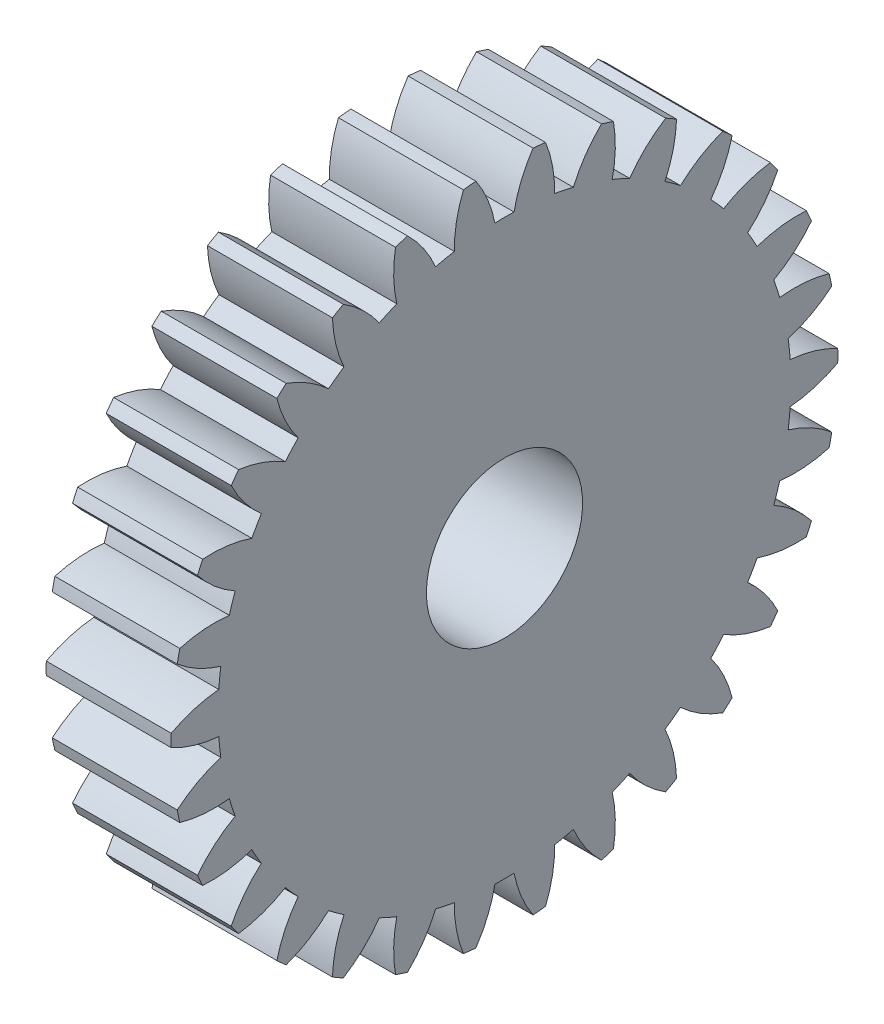
SolidWorks part; units mm, degrees
ref_plane "Plane1" through (0, 0, 0) normal (0, 0, 1) x (1, 0, 0)
ref_plane "Plane2" through (0, 0, 0) normal (0, 1, 0) x (1, 0, 0)
ref_plane "Plane3" through (0, 0, 0) normal (1, 0, 0) x (0, 0, -1)
other "Configuration Table"
sketch "HoldingSke" plane through (0, 0, 0) normal (0, 1, 0) x (1, 0, 0)
  line L0 (0, 0) -> (0.433, -0.25)
  line L1 (-15, 0) -> (100, 0) construction
  line L2 (0, 0) -> (-2.1039, 2.3779)
  line L3 (0, 0) -> (-11.863, 4.5341)
  line L4 (0, 0) -> (7.479, 4.318)
  line L5 (0, 0) -> (-46.8476, -17.4728)
  line L6 (0, 0) -> (-9.9476, -6.7116)
  line L7 (-2.1039, 2.3779) -> (8.6586, 51.2059)
  line L8 (-76.2, 54.61) -> (-73.9, 54.61)
  line L9 (-71.009, 38.7566) -> (-53.1078, 45.2721)
  line L10 (-76.2, 71.12) -> (104.1128, 71.12)
  line L11 (0, 0) -> (-12, 0)
  line L12 (-76.2, 101.6) -> (-76.133, 101.6)
  line L13 (24.9733, 27.94) -> (52.9518, 28.4284)
  line L14 (24.9733, 27.94) -> (24.9743, 27.94)
  line L15 (24.9733, 27.94) -> (100.4006, 29.5858)
  line L16 (-63.627, -2) -> (-12.827, -2)
  circle A0 centre (0, 0) radius 7.5
  circle A1 centre (0, 0) radius 27.499
  circle A2 centre (0, 0) radius 37.5
  circle A3 centre (0, 0) radius 7.5
  dimension "MHD" = 54.998
  dimension "Hub_dia" = 75
  dimension "Bore" = 15
  dimension "MBD" = 15
  dimension "Num_teeth" = 30
  dimension "Pitch" = 0.5
  dimension "Overall_len" = 50
  dimension "Show_teeth" = 30
  dimension "Thickness" = 12
  dimension "OAL" = 50.0001
  dimension "T_dim" = 2.3
  dimension "Ap" = 20
  dimension "H" = 19.05
  dimension "Pitch_radius" = 180.3128
  dimension "Width" = 12
  dimension "Backlash" = 0.067
  dimension "Addendum_fac" = 1
  dimension "Dedendum_fac" = 1.25
  dimension "Clearance_fac" = 0.25
  dimension "Dedendum_add" = 0.001
  dimension "Module" = 2
sketch "BasProSke" plane through (0, 0, 0) normal (0, 1, 0) x (1, 0, 0)
  line L0 (-10, 0) -> (60, 0) construction
  line L1 (0, 0) -> (0, 32)
  line L2 (0, 0) -> (12, 0)
  line L3 (12, 0) -> (12, 32)
  line L4 (12, 32) -> (0, 32)
  dimension "Thickness" = 12
  dimension "Diameter" = 64
revolve "Base-Revolve" add sketch "BasProSke" angle 360 about L0
sketch "TooCutSke" plane through (0, 0, 0) normal (1, 0, 0) x (0, 0, -1)
  line L1 (0, 0) -> (0, 107) construction
  line L2 (0, 0) -> (-1.6873, 29.9525) construction
  line L3 (0, 0) -> (-6.2643, 59.6013) construction
  line L4 (-1.6873, 29.9525) -> (-3.1322, 29.8007) construction
  arc A0 (0.9186, 27.4837) -> (-0.9186, 27.4837) centre (0, 0) ccw
  arc A1 (2.7618, 31.9061) -> (-2.7618, 31.9061) centre (0, 0) ccw
  circle A2 centre (0, 0) radius 30 construction
  circle A3 centre (0, 0) radius 28.1908 construction
  arc A4 (-0.9186, 27.4837) -> (-2.7618, 31.9061) centre (-12.6936, 25.1712) ccw
  arc A5 (2.7618, 31.9061) -> (0.9186, 27.4837) centre (12.6936, 25.1712) ccw
  dimension "Root_dia" = 54.998
  dimension "Overcut_dia" = 64.0508
  dimension "Pitch_dia" = 60
  dimension "Base_dia" = 56.3816
  dimension "Flank_rad" = 12
  dimension "Half_ang" = 6
  dimension "Half_CT" = 1.4528
extrude "ToothCut" cut sketch "TooCutSke" along normal through all
fillet "Breaks" [suppressed] radius 0.04
fillet "RootFillets" [suppressed] radius 0.501
pattern_circular "TeethCuts" count 30 every 12 about axis through (-10, 0, 0) along (1, 0, 0) of "ToothCut"
sketch "HubNeaOneSke" plane through (0, 0, 0) normal (-1, 0, 0) x (0, 0, 1)
  circle A0 centre (0, 0) radius 27.499
  dimension "Diameter" = 54.998
extrude "HubNearOne" [suppressed] add sketch "HubNeaOneSke" along normal blind 38.0001
sketch "HubNeaBotSke" plane through (0, 0, 0) normal (-1, 0, 0) x (0, 0, 1)
  circle A0 centre (0, 0) radius 27.499
  dimension "Diameter" = 54.998
extrude "HubNearBoth" [suppressed] add sketch "HubNeaBotSke" along normal blind 19
ref_plane "FarPln" through (12, 0, 0) normal (1, 0, 0) x (0, 0, -1)
sketch "HubFarSke" plane through (12, 0, 0) normal (1, 0, 0) x (0, 0, -1)
  circle A0 centre (0, 0) radius 27.499
  dimension "Diameter" = 54.998
extrude "HubFar" [suppressed] add sketch "HubFarSke" along normal blind 19
sketch "BorSke" plane through (0, 0, 0) normal (1, 0, 0) x (0, 0, -1)
  circle A0 centre (0, 0) radius 7.5
  dimension "Diameter" = 15
extrude "Bore" cut sketch "BorSke" along normal mid plane 100.0001
sketch "KeySke" plane through (0, 0, 0) normal (1, 0, 0) x (0, 0, -1)
  line L0 (-2.5, 0) -> (-2.5, 9.8)
  line L1 (-2.5, 9.8) -> (2.5, 9.8)
  line L2 (2.5, 9.8) -> (2.5, 0)
  line L3 (0, 0) -> (0, 34) construction
  line L4 (-2.5, 0) -> (2.5, 0)
  dimension "Offset" = 9.8
  dimension "Width" = 5
extrude "Keyway" [suppressed] cut sketch "KeySke" along normal mid plane 100.0001
pattern_circular "Keyway2" [suppressed] count 2 every 90 about axis through (-10, 0, 0) along (1, 0, 0)
equation "' \"Module@HoldingSke\" = 6.35"
equation "' \"Num_teeth@HoldingSke\" = 12"
equation "' \"Ap@HoldingSke\" =  20"
equation "' \"Ap@HoldingSke\" = 20"
equation "' \"Width@HoldingSke\" = 0.5 * 25.4"
equation "' \"Hub_dia@HoldingSke\"= 1 * 25.4"
equation "' \"Hub_dia@HoldingSke\" = 1 * 25.4"
equation "' \"Overall_len@HoldingSke\" = 1.0 * 25.4"
equation "' \"Bore@HoldingSke\" = 0.75 * 25.4"
equation "' \"T_dim@HoldingSke\" = 0.1 * 25.4"
equation "' \"Width@KeySke\" = 0.25 * 25.4"
equation "' \"Show_teeth@HoldingSke\" = 13"
equation "' \"Backlash@HoldingSke\" = 0.009 * 25.4"
equation "' \"Addendum_fac@HoldingSke\" = 1.0"
equation "' \"Dedendum_fac@HoldingSke\" = 1.25"
equation "' \"Dedendum_add@HoldingSke\" = 0.00005 * 25.4"
equation "' \"Clearance_fac@HoldingSke\" = 0.25"
equation "\"Pitch@HoldingSke\" = 1 / \"Module@HoldingSke\""
equation "\"Overcut_dia@TooCutSke\" = (\"Num_teeth@HoldingSke\" + 2 * \"Addendum_fac@HoldingSke\") / \"Pitch@HoldingSke\" + 0.002 * 25.4"
equation "\"Pitch_dia@TooCutSke\" = \"Num_teeth@HoldingSke\" / \"Pitch@HoldingSke\""
equation "\"Base_dia@TooCutSke\" = \"Num_teeth@HoldingSke\" / \"Pitch@HoldingSke\" * cos((\"Ap@HoldingSke\"  * 3.14159265 / 180))"
equation "\"Root_dia@TooCutSke\" = (\"Num_teeth@HoldingSke\" + 2) / \"Pitch@HoldingSke\" - 2 * (\"Addendum_fac@HoldingSke\" + \"Dedendum_fac@HoldingSke\") / \"Pitch@HoldingSke\" - \"Dedendum_add@HoldingSke\" * 2"
equation "\"Half_ang@TooCutSke\" = 180 / \"Num_teeth@HoldingSke\""
equation "\"Half_CT@TooCutSke\" = \"Num_teeth@HoldingSke\" / \"Pitch@HoldingSke\" * sin((3.14159265 / 2 / \"Num_teeth@HoldingSke\")) / 2 - 7 * \"Backlash@HoldingSke\" / 4"
equation "\"Flank_rad@TooCutSke\" = \"Num_teeth@HoldingSke\" / \"Pitch@HoldingSke\" / 5"
equation "\"Radius@RootFillets\" = \"Clearance_fac@HoldingSke\" / \"Pitch@HoldingSke\" + \"Dedendum_add@HoldingSke\""
equation "\"Break_rad@Breaks\" = 0.02 / \"Pitch@HoldingSke\""
equation "\"Thickness@HoldingSke\" = \"Width@HoldingSke\""
equation "\"OAL@HoldingSke\" = \"Thickness@HoldingSke\""
equation "\"MHD@HoldingSke\" = (\"Num_teeth@HoldingSke\" + 2) / \"Pitch@HoldingSke\" - 2 * (\"Addendum_fac@HoldingSke\" + \"Dedendum_fac@HoldingSke\")  / \"Pitch@HoldingSke\" - \"Dedendum_add@HoldingSke\" * 2"
equation "\"MBD@HoldingSke\" = (\"Num_teeth@HoldingSke\" + 2) / \"Pitch@HoldingSke\" - 2 * (\"Addendum_fac@HoldingSke\" + \"Dedendum_fac@HoldingSke\")  / \"Pitch@HoldingSke\" - \"Dedendum_add@HoldingSke\" * 2 - 0.002 * 25.4"
equation "\"MHD@HoldingSke\" = ((sgn( \"MHD@HoldingSke\" - \"Hub_dia@HoldingSke\" )-1)*( \"MHD@HoldingSke\" - \"Hub_dia@HoldingSke\" ))/-2+ \"Hub_dia@HoldingSke\""
equation "\"MBD@HoldingSke\" = ((sgn( \"MBD@HoldingSke\" - \"Bore@HoldingSke\" )-1)*( \"MBD@HoldingSke\" - \"Bore@HoldingSke\" ))/-2+ \"Bore@HoldingSke\""
equation "\"OAL@HoldingSke\" = ((sgn( \"OAL@HoldingSke\" - \"Overall_len@HoldingSke\" )+1)*( \"OAL@HoldingSke\" - \"Overall_len@HoldingSke\" ))/2 + \"Overall_len@HoldingSke\" + 0.000002 * 25.4"
equation "\"Num_teeth@TeethCuts\" = int( \"Show_teeth@HoldingSke\" ) + 1"
equation "\"Num_teeth@TeethCuts\" = ((sgn( \"Num_teeth@TeethCuts\" - \"Num_teeth@HoldingSke\" )-1)*( \"Num_teeth@TeethCuts\" - \"Num_teeth@HoldingSke\" ))/-2+ \"Num_teeth@HoldingSke\""
equation "\"Num_teeth@TeethCuts\" = ((sgn( \"Num_teeth@TeethCuts\" - 2.0)+1)*( \"Num_teeth@TeethCuts\" - 2.0))/2 +2.0"
equation "\"Angle@TeethCuts\" = 360.0 / \"Num_teeth@HoldingSke\""
equation "\"Diameter@BasProSke\" = (\"Num_teeth@HoldingSke\" + 2 * \"Addendum_fac@HoldingSke\") / \"Pitch@HoldingSke\""
equation "\"Thickness@BasProSke\"  = \"Thickness@HoldingSke\""
equation "' \"Fillet_rad@BasProSke\" =  \"Thickness@HoldingSke\" * 0.05"
equation "' \"Fillet_rad@BasProSke\" = \"Thickness@HoldingSke\" * 0.05"
equation "\"MHD@HoldingSke\" = ((sgn( \"MHD@HoldingSke\" - \"Root_dia@TooCutSke\" )-1)*( \"MHD@HoldingSke\" - \"Root_dia@TooCutSke\" ))/-2+ \"Root_dia@TooCutSke\""
equation "\"Diameter@HubNeaOneSke\" = \"MHD@HoldingSke\""
equation "\"Length@HubNearOne\" = \"OAL@HoldingSke\" - \"Thickness@BasProSke\""
equation "\"Diameter@HubNeaBotSke\" = \"MHD@HoldingSke\""
equation "\"Length@HubNearBoth\" = ( \"OAL@HoldingSke\" - \"Thickness@BasProSke\" ) / 2.0"
equation "\"Thickness@FarPln\" = \"Thickness@BasProSke\""
equation "\"Diameter@HubFarSke\" = \"MHD@HoldingSke\""
equation "\"Length@HubFar\" = ( \"OAL@HoldingSke\" - \"Thickness@BasProSke\" ) / 2.0"
equation "\"Diameter@BorSke\" = \"MBD@HoldingSke\""
equation "\"D1@Bore\" = \"OAL@HoldingSke\" * 2.0"
equation "\"D1@Keyway\" = \"OAL@HoldingSke\" * 2.0"
equation "\"Offset@KeySke\" = \"T_dim@HoldingSke\" + \"MBD@HoldingSke\" / 2.0"
